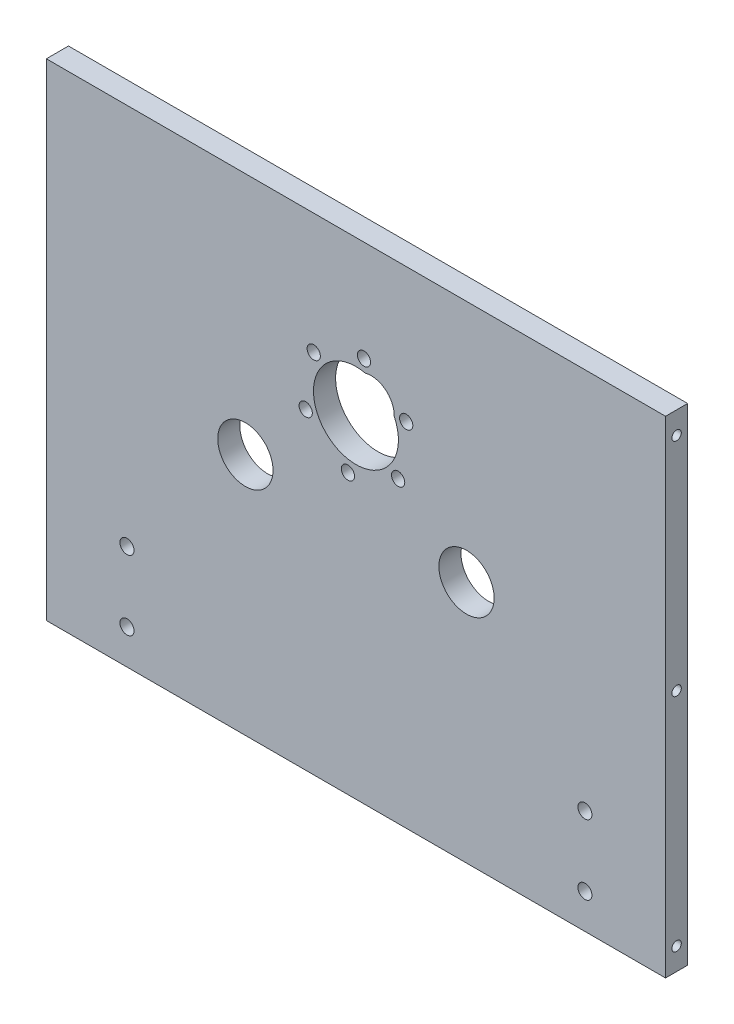
SolidWorks part; units mm, degrees
material "6061 Alloy"
ref_plane "Front Plane" through (0, 0, 0) normal (0, 0, 1) x (1, 0, 0)
ref_plane "Top Plane" through (0, 0, 0) normal (0, 1, 0) x (1, 0, 0)
ref_plane "Right Plane" through (0, 0, 0) normal (1, 0, 0) x (0, 0, -1)
sketch "Sketch1" plane through (0, 0, 0) normal (0, 0, 1) x (1, 0, 0)
  line L1 (-88.9, -69.85) -> (88.9, -69.85)
  line L2 (-88.9, -69.85) -> (-88.9, 69.85)
  line L3 (-88.9, 69.85) -> (88.9, 69.85)
  line L4 (88.9, -69.85) -> (88.9, 69.85)
  line L5 (-88.9, -69.85) -> (88.9, 69.85) construction
  line L6 (-88.9, 69.85) -> (88.9, -69.85) construction
  point P0 (0, 0)
  dimension "D1" = 177.8
  dimension "D2" = 139.7
extrude "Boss-Extrude1" add sketch "Sketch1" along normal blind 6.35
sketch "Sketch2" plane through (0, 0, 6.35) normal (0, 0, 1) x (1, 0, 0)
  line L0 (-31.75, 0) -> (31.75, 0) construction
  line L1 (0, -3.4925) -> (0, 3.4925) construction
  circle A0 centre (-31.75, 0) radius 7.9375
  circle A1 centre (31.75, 0) radius 7.9375
  point P4 (0, 0)
  dimension "D2" = 15.875
  dimension "D1" = 63.5
extrude "Cut-Extrude1" cut sketch "Sketch2" against normal through all
sketch "Sketch3" plane through (0, 0, 6.35) normal (0, 0, 1) x (1, 0, 0)
  line L1 (-57.15, -31.75) -> (57.15, -31.75)
  line L2 (-57.15, -31.75) -> (-57.15, 31.75)
  line L3 (-57.15, 31.75) -> (57.15, 31.75)
  line L4 (57.15, -31.75) -> (57.15, 31.75)
  line L5 (-57.15, -31.75) -> (57.15, 31.75) construction
  line L6 (-57.15, 31.75) -> (57.15, -31.75) construction
  point P0 (0, 0)
  dimension "D1" = 114.3
  dimension "D2" = 63.5
sketch "Sketch5" plane through (88.9, 0, 0) normal (1, 0, 0) x (0, 0, -1)
  line L0 (-3.175, -41.275) -> (-3.175, 41.275)
  line L1 (-6.35, 69.85) -> (0, 69.85) construction
  line L2 (0, -69.85) -> (0, 69.85) construction
  point P3 (-3.175, 0)
  point P5 (-3.175, 69.85)
  point P9 (0, 0)
  dimension "D1" = 82.55
sketch "Sketch8" plane through (0, 69.85, 0) normal (0, 1, 0) x (1, 0, 0)
  line L0 (-57.15, -3.175) -> (57.15, -3.175)
  line L1 (0, -3.4925) -> (0, 3.4925) construction
  line L2 (-88.9, -6.35) -> (-88.9, 0) construction
  point P3 (0, -3.175)
  point P8 (-88.9, -3.175)
  dimension "D1" = 114.3
sketch "Sketch10" [suppressed] plane through (0, 0, 6.35) normal (0, 0, 1) x (1, 0, 0)
  line L0 (-4.3638, -31.0503) -> (4.3638, 31.0503) construction
  line L1 (-88.9, -69.85) -> (88.9, -69.85) construction
  circle A0 centre (31.75, 0) radius 7.9375 construction
  circle A2 centre (4.3638, 31.0503) radius 4.5
  circle A3 centre (-4.3638, -31.0503) radius 4.5 construction
  point P4 (0, 0)
  dimension "D1" = 41.402
  dimension "D2" = 82
  dimension "D3" = 9
extrude "Cut-Extrude2" [suppressed] cut sketch "Sketch10" against normal through all
sketch "Sketch11" [suppressed] plane through (0, 0, 6.35) normal (0, 0, 1) x (1, 0, 0)
  circle A0 centre (31.75, 0) radius 7.9375 construction
  circle A1 centre (-31.75, 0) radius 7.9375 construction
  circle A2 centre (31.75, 0) radius 7.9375
  circle A3 centre (-31.75, 0) radius 7.9375
extrude "Boss-Extrude2" [suppressed] add sketch "Sketch11" against normal up to surface (6.35 mm away)
sketch "Sketch12" plane through (0, 0, 6.35) normal (0, 0, 1) x (1, 0, 0)
  line L1 (-95.25, 50.8) -> (-88.9, 50.8)
  line L2 (-95.25, 50.8) -> (-95.25, 69.85)
  line L3 (-95.25, 69.85) -> (-88.9, 69.85)
  line L4 (-88.9, 50.8) -> (-88.9, 69.85)
  line L5 (-95.25, 50.8) -> (-88.9, 69.85) construction
  line L6 (-95.25, 69.85) -> (-88.9, 50.8) construction
  point P0 (-92.075, 60.325)
  dimension "D1" = 19.05
  dimension "D2" = 6.35
extrude "Boss-Extrude3" [suppressed] add sketch "Sketch12" against normal up to surface (6.35 mm away)
pattern_linear "LPattern1" [suppressed] count 4 spacing 38.1
mirror "Mirror1" [suppressed] about plane through (0, 0, 0) normal (1, 0, 0)
sketch "Sketch13" plane through (0, 0, 6.35) normal (0, 0, 1) x (1, 0, 0)
  circle A1 centre (4.3638, 31.0503) radius 16.129
  dimension "D1" = 32.258
  dimension "D2" = 31.0503
  dimension "D3" = 4.3638
extrude "Cut-Extrude3" [suppressed] cut sketch "Sketch13" against normal through all
hole_wizard "#10 Clearance Hole1" [suppressed] positions "Sketch14" profile "Sketch15" hole size "#10" standard "ANSI Inch"
sketch "Sketch14" plane through (0, 0, 6.35) normal (0, 0, 1) x (1, 0, 0)
  circle A3 centre (4.3638, 51.2559) radius 2.0193 construction
  circle A4 centre (-15.8417, 31.0503) radius 2.0193 construction
  circle A5 centre (24.5694, 31.0503) radius 2.0193 construction
  circle A6 centre (4.3638, 10.8448) radius 2.0193 construction
  point P0 (4.3638, 51.2559)
  point P2 (-15.8417, 31.0503)
  point P5 (24.5694, 31.0503)
  point P7 (4.3638, 10.8448)
sketch "Sketch15" plane through (4.3638, 51.2559, 6.35) normal (1, 0, 0) x (0, -1, 0)
  line L0 (0, 0) -> (0, 6.35)
  line L1 (0, 6.35) -> (2.5527, 6.35)
  line L2 (2.5527, 6.35) -> (2.5527, 0)
  line L5 (2.5527, 0) -> (0, 0)
  line L11 (0, -6.35) -> (0, 107.95) construction
  dimension "Thru Hole Dia." = 5.1054
  dimension "Thru Hole Depth" = 6.35
hole_wizard "Tap Drill for #6-32 Tap1" positions "Sketch16" profile "Sketch17" hole size "#6-32" standard "ANSI Inch"
sketch "Sketch16" plane through (88.9, 0, 0) normal (1, 0, 0) x (0, 0, -1)
  line L0 (0, -69.85) -> (0, 69.85) construction
  point P0 (-3.175, 63.5)
  point P2 (-3.175, 0)
  point P4 (-3.175, -63.5)
  dimension "D1" = 3.175
  dimension "D2" = 63.5
  dimension "D3" = 63.5
sketch "Sketch17" plane through (88.9, 63.5, 3.175) normal (0, 1, 0) x (0, 0, -1)
  line L0 (0, 0) -> (0, 13.5127)
  line L1 (0, 13.5127) -> (1.3525, 12.7)
  line L2 (1.3525, 12.7) -> (1.3525, 0)
  line L5 (1.3525, 0) -> (0, 0)
  line L10 (0, 13.5127) -> (-1.3526, 12.7) construction
  line L11 (0, -6.35) -> (0, 107.95) construction
  dimension "Hole Dia." = 2.7051
  dimension "Hole Depth" = 12.7
  dimension "Drill Angle" = 118
mirror "Mirror2" about plane through (0, 0, 0) normal (1, 0, 0) of "Tap Drill for #6-32 Tap1"
hole_wizard "Tap Drill for #10-32 Tap1" positions "Sketch18" profile "Sketch19" hole size "#10-32" standard "ANSI Inch" end condition through all
sketch "Sketch18" plane through (0, 0, 6.35) normal (0, 0, 1) x (1, 0, 0)
  line L0 (-88.9, -69.85) -> (88.9, -69.85) construction
  line L1 (-88.9, 69.85) -> (-88.9, -69.85) construction
  point P0 (-65.75, -59.85)
  point P2 (-65.75, -39.85)
  dimension "D1" = 10
  dimension "D2" = 23.15
  dimension "D3" = 20
sketch "Sketch19" plane through (-65.75, -59.85, 6.35) normal (1, 0, 0) x (0, -1, 0)
  line L0 (0, 0) -> (0, 6.35)
  line L1 (0, 6.35) -> (2.0193, 6.35)
  line L2 (2.0193, 6.35) -> (2.0193, 0)
  line L5 (2.0193, 0) -> (0, 0)
  line L11 (0, -6.35) -> (0, 107.95) construction
  dimension "Thru Hole Dia." = 4.0386
  dimension "Thru Hole Depth" = 6.35
mirror "Mirror3" about plane through (0, 0, 0) normal (1, 0, 0) of "Tap Drill for #10-32 Tap1"
sketch "Sketch20" plane through (0, 0, 6.35) normal (0, 0, 1) x (1, 0, 0)
  circle A0 centre (0, 25.5771) radius 12.192
  arc A1 (-14.3869, 37.0477) -> (14.3869, 14.1064) centre (0, 25.5771) ccw construction
  dimension "D1" = 24.384
extrude "Cut-Extrude4" cut sketch "Sketch20" against normal through all
hole_wizard "#6 Clearance Hole1" positions "Sketch21" profile "Sketch22" hole size "#6" standard "ANSI Inch" end condition through all
sketch "Sketch21" plane through (0, 0, 6.35) normal (0, 0, 1) x (1, 0, 0)
  arc A0 (1.3311, 41.6834) -> (3.2859, 40.1249) centre (2.3085, 40.9042) ccw construction
  point P0 (2.3085, 40.9042)
sketch "Sketch22" plane through (2.3085, 40.9042, 6.35) normal (1, 0, 0) x (0, -1, 0)
  line L0 (0, 0) -> (0, 6.35)
  line L1 (0, 6.35) -> (1.8986, 6.35)
  line L2 (1.8986, 6.35) -> (1.8986, 0)
  line L5 (1.8986, 0) -> (0, 0)
  line L11 (0, -6.35) -> (0, 107.95) construction
  dimension "Thru Hole Dia." = 3.7973
  dimension "Thru Hole Depth" = 6.35
pattern_circular "CirPattern1" count 6 over 360 about axis through (0, 25.5771, 0) along (0, 0, 1) of "#6 Clearance Hole1"
sketch "Sketch23" plane through (0, 0, 0) normal (0, 0, -1) x (-1, 0, 0)
  arc A4 (0.8241, 35.1866) -> (-9.5517, 26.914) centre (-4.3638, 31.0503) ccw
  arc A5 (-9.5517, 26.914) -> (0.8241, 35.1866) centre (-4.3638, 31.0503) ccw
  arc A6 (0.8241, 35.1866) -> (-9.5517, 26.914) centre (-4.3638, 31.0503) ccw
  arc A7 (-9.5517, 26.914) -> (0.8241, 35.1866) centre (-4.3638, 31.0503) ccw
  dimension "D1" = 0.635
extrude "Cut-Extrude5" cut sketch "Sketch23" against normal through all
equation "\"thicc\"= .25"
equation "\"D1@Sketch16\"=\"thicc\"/2"
equation "\"hole_dist\"=2.5"
equation "\"D2@Sketch16\"=\"hole_dist\""
equation "\"D3@Sketch16\"=\"hole_dist\""
